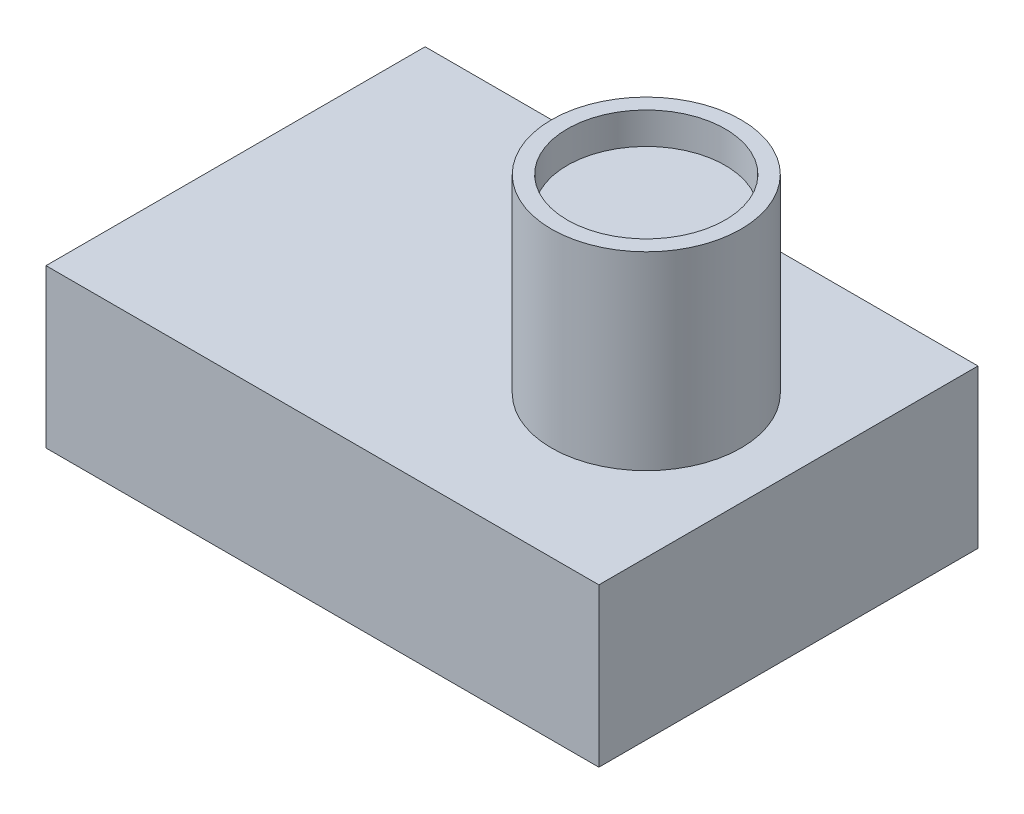
SolidWorks part; units mm, degrees
material "1060 Alloy"
ref_plane "Front Plane" through (0, 0, 0) normal (0, 0, 1) x (1, 0, 0)
ref_plane "Top Plane" through (0, 0, 0) normal (0, 1, 0) x (1, 0, 0)
ref_plane "Right Plane" through (0, 0, 0) normal (1, 0, 0) x (0, 0, -1)
sketch "Sketch2" plane through (0, 0, 0) normal (0, 1, 0) x (1, 0, 0)
  line L1 (-17.5, 12) -> (17.5, 12)
  line L2 (-17.5, 12) -> (-17.5, -12)
  line L3 (-17.5, -12) -> (17.5, -12)
  line L4 (17.5, 12) -> (17.5, -12)
  line L5 (-17.5, 12) -> (17.5, -12) construction
  line L6 (-17.5, -12) -> (17.5, 12) construction
  point P0 (0, 0)
  dimension "D1" = 35
  dimension "D2" = 24
extrude "Boss-Extrude1" add sketch "Sketch2" along normal blind 10
sketch "Sketch3" plane through (0, 10, 0) normal (0, 1, 0) x (1, 0, 0)
  line L0 (17.5, -12) -> (17.5, 12) construction
  circle A0 centre (8.5, 0) radius 6
  dimension "D1" = 12
  dimension "D2" = 9
extrude "Boss-Extrude2" add sketch "Sketch3" along normal blind 12
sketch "Sketch4" plane through (0, 22, 0) normal (0, 1, 0) x (1, 0, 0)
  circle A0 centre (8.5, 0) radius 5
  circle A1 centre (8.5, 0) radius 6 construction
  dimension "D1" = 10
extrude "Cut-Extrude2" cut sketch "Sketch4" against normal blind 2
